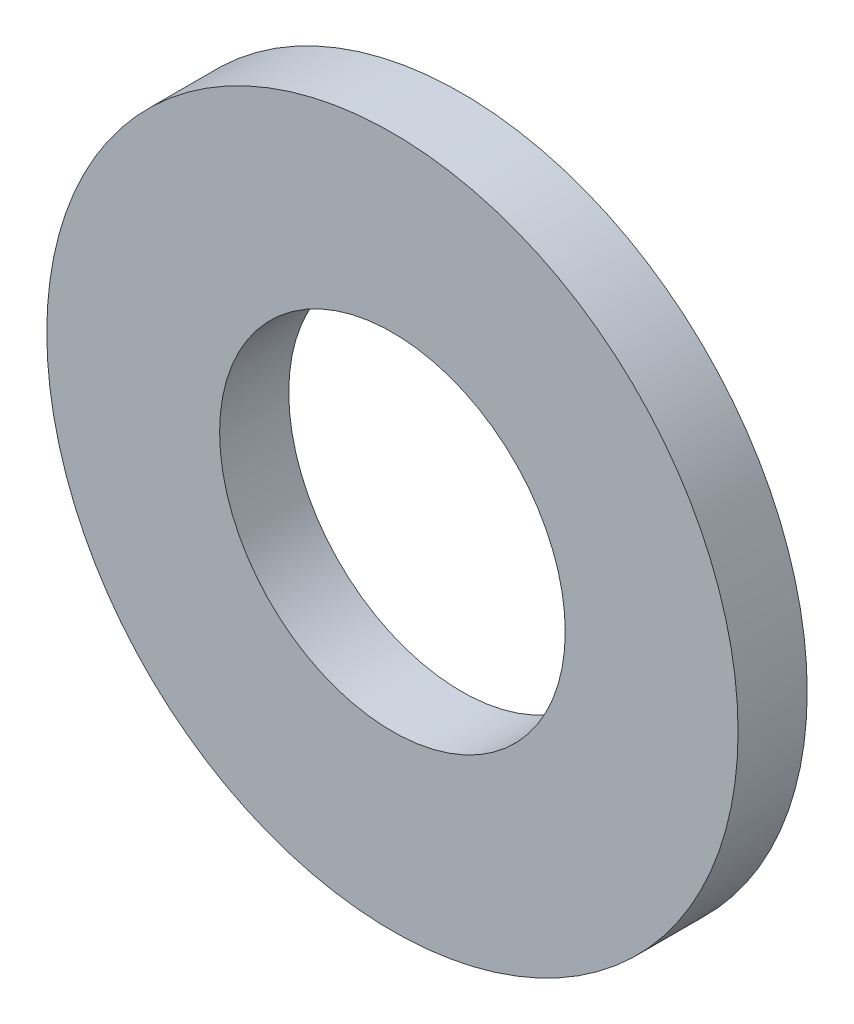
SolidWorks part; units mm, degrees
ref_plane "Front Plane" through (0, 0, 0) normal (0, 0, 1) x (1, 0, 0)
ref_plane "Top Plane" through (0, 0, 0) normal (0, 1, 0) x (1, 0, 0)
ref_plane "Right Plane" through (0, 0, 0) normal (1, 0, 0) x (0, 0, -1)
sketch "Sketch1" plane through (0, 0, 0) normal (0, 0, 1) x (1, 0, 0)
  circle A0 centre (0, 0) radius 7.9375
  circle A1 centre (0, 0) radius 3.9688
  dimension "D1" = 7.9375
  dimension "D2" = 15.875
extrude "Boss-Extrude1" add sketch "Sketch1" along normal blind 1.5875
